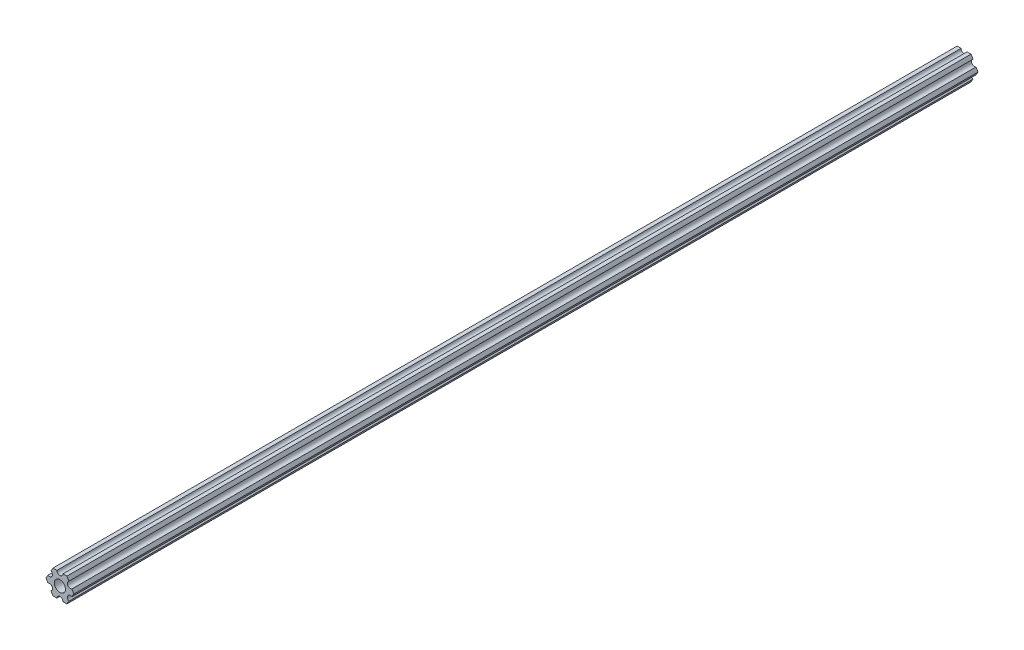
SolidWorks part; units mm, degrees
ref_plane "Front Plane" through (0, 0, 0) normal (0, 0, 1) x (1, 0, 0)
ref_plane "Top Plane" through (0, 0, 0) normal (0, 1, 0) x (1, 0, 0)
ref_plane "Right Plane" through (0, 0, 0) normal (1, 0, 0) x (0, 0, -1)
ref_plane "Plane1" through (0, 0, 0) normal (0, 0, -1) x (-1, 0, 0)
sketch "Sketch1" plane through (0, 0, 0) normal (0, 0, -1) x (-1, 0, 0)
  line L0 (-4.7055, -4.5498) -> (-3.6662, -6.35)
  line L1 (-3.6662, -6.35) -> (-1.5875, -6.35)
  line L2 (1.5875, -6.35) -> (3.6662, -6.35)
  line L3 (3.6662, -6.35) -> (4.7055, -4.5498)
  line L4 (6.293, -1.8002) -> (7.3323, 0)
  line L5 (7.3323, 0) -> (6.293, 1.8002)
  line L6 (4.7055, 4.5498) -> (3.6662, 6.35)
  line L7 (3.6662, 6.35) -> (1.5875, 6.35)
  line L8 (-1.5875, 6.35) -> (-3.6662, 6.35)
  line L9 (-3.6662, 6.35) -> (-4.7055, 4.5498)
  line L10 (-6.293, 1.8002) -> (-7.3323, 0)
  line L11 (-7.3323, 0) -> (-6.293, -1.8002)
  circle A0 centre (0, 0) radius 2.9337
  arc A1 (-6.293, -1.8002) -> (-4.7055, -4.5498) centre (-5.4993, -3.175) cw
  arc A2 (-1.5875, -6.35) -> (1.5875, -6.35) centre (0, -6.35) cw
  arc A3 (4.7055, -4.5498) -> (6.293, -1.8002) centre (5.4993, -3.175) cw
  arc A4 (6.293, 1.8002) -> (4.7055, 4.5498) centre (5.4993, 3.175) cw
  arc A5 (1.5875, 6.35) -> (-1.5875, 6.35) centre (0, 6.35) cw
  arc A6 (-4.7055, 4.5498) -> (-6.293, 1.8002) centre (-5.4993, 3.175) cw
extrude "Boss-Extrude1" add sketch "Sketch1" against normal blind 476.25
